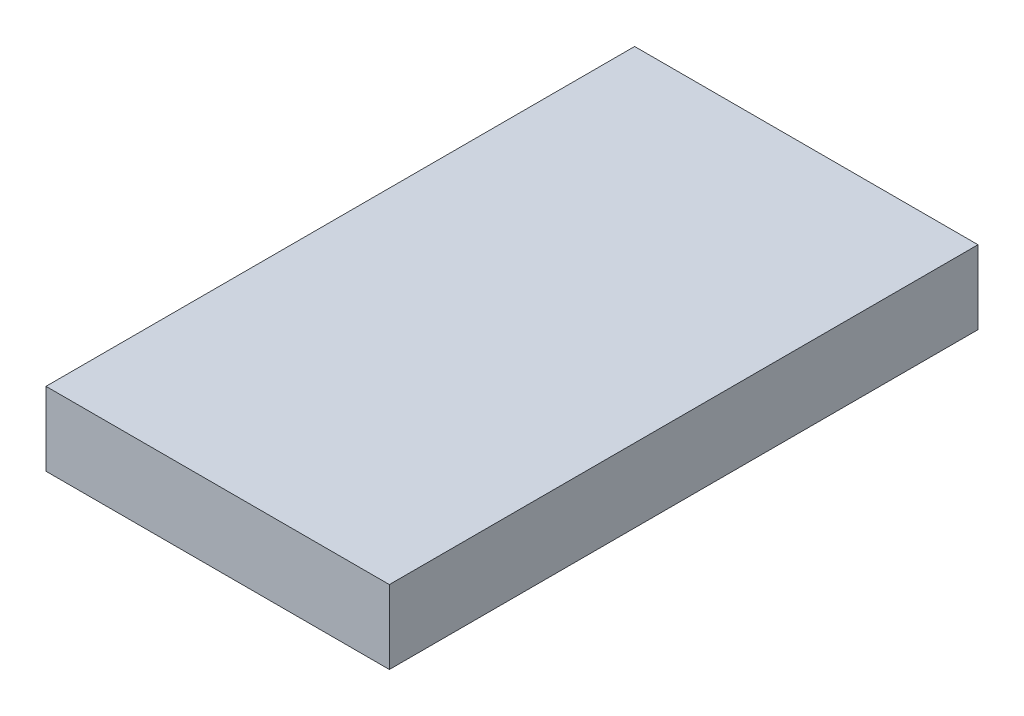
SolidWorks part; units mm, degrees
ref_plane "Front Plane" through (0, 0, 0) normal (0, 0, 1) x (1, 0, 0)
ref_plane "Top Plane" through (0, 0, 0) normal (0, 1, 0) x (1, 0, 0)
ref_plane "Right Plane" through (0, 0, 0) normal (1, 0, 0) x (0, 0, -1)
sketch "Sketch1" plane through (0, 0, 0) normal (0, 1, 0) x (1, 0, 0)
  line L1 (0, 0) -> (35.56, 0)
  line L2 (0, 0) -> (0, 60.96)
  line L3 (0, 60.96) -> (35.56, 60.96)
  line L4 (35.56, 0) -> (35.56, 60.96)
  dimension "D1" = 60.96
  dimension "D2" = 35.56
extrude "Boss-Extrude1" add sketch "Sketch1" along normal blind 7.62
